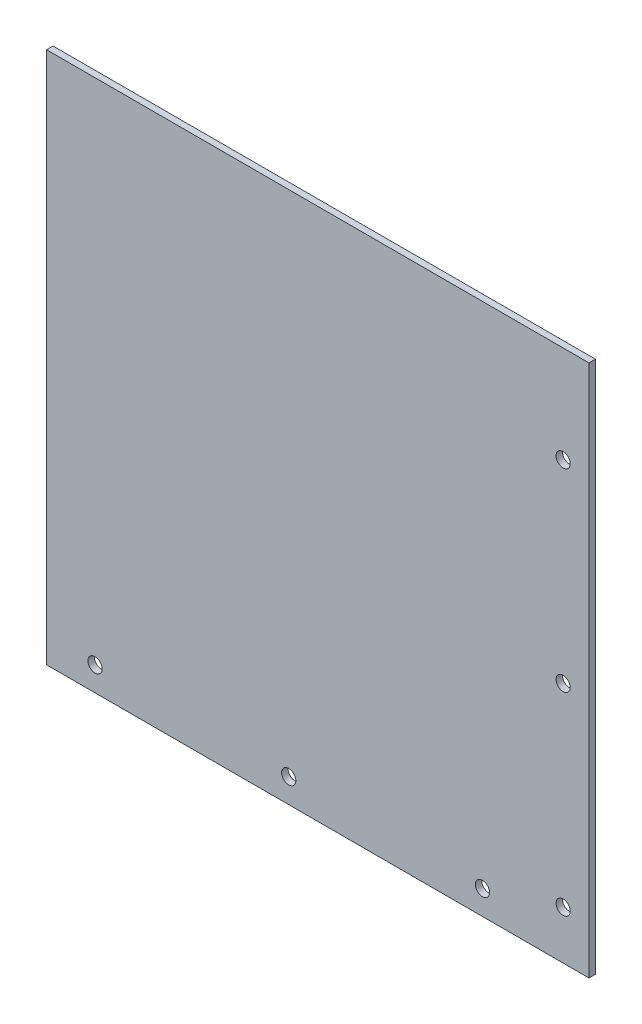
SolidWorks part; units mm, degrees
ref_plane "正面" through (0, 0, 0) normal (0, 0, 1) x (1, 0, 0)
ref_plane "平面" through (0, 0, 0) normal (0, 1, 0) x (1, 0, 0)
ref_plane "右側面" through (0, 0, 0) normal (1, 0, 0) x (0, 0, -1)
sketch "ｽｹｯﾁ1" plane through (0, 0, 0) normal (0, 0, 1) x (1, 0, 0)
  line L1 (-84, 83.5) -> (84, 83.5)
  line L2 (-84, 83.5) -> (-84, -83.5)
  line L3 (-84, -83.5) -> (84, -83.5)
  line L4 (84, 83.5) -> (84, -83.5)
  line L5 (-84, 83.5) -> (84, -83.5) construction
  line L6 (-84, -83.5) -> (84, 83.5) construction
  point P0 (0, 0)
  dimension "D1" = 167
  dimension "D2" = 168
extrude "ﾎﾞｽ - 押し出し1" add sketch "ｽｹｯﾁ1" along normal blind 2
sketch "ｽｹｯﾁ2" plane through (0, 0, 2) normal (0, 0, 1) x (1, 0, 0)
  line L0 (84, -83.5) -> (76, -83.5)
  line L1 (-84, -83.5) -> (84, -83.5) construction
  line L2 (76, -83.5) -> (76, -68.5)
  line L3 (76, -68.5) -> (76, -20.6241)
  line L4 (76, -83.5) -> (76, -8.5)
  line L5 (76, -83.5) -> (76, 51.5)
  circle A0 centre (76, -68.5) radius 2.2
  circle A1 centre (76, -8.5) radius 2.2
  circle A2 centre (76, 51.5) radius 2.2
  dimension "D5" = 4.4
  dimension "D6" = 4.4
  dimension "D7" = 4.4
  dimension "D1" = 8
  dimension "D2" = 15
  dimension "D3" = 75
  dimension "D4" = 135
extrude "ｶｯﾄ - 押し出し1" cut sketch "ｽｹｯﾁ2" against normal blind 2
sketch "ｽｹｯﾁ3" plane through (0, 83.5, 0) normal (0, 1, 0) x (1, 0, 0)
  line L1 (-84, -2) -> (84, -2)
  line L2 (-84, -2) -> (-84, 0)
  line L3 (-84, 0) -> (84, 0)
  line L4 (84, -2) -> (84, 0)
extrude "ｶｯﾄ - 押し出し2" cut sketch "ｽｹｯﾁ3" against normal blind 2
sketch "ｽｹｯﾁ4" plane through (0, 0, 2) normal (0, 0, 1) x (1, 0, 0)
  line L0 (-84, -83.5) -> (-84, -76)
  line L1 (-84, 81.5) -> (-84, -83.5) construction
  line L2 (-84, -76) -> (-69, -76)
  line L3 (-84, -76) -> (-9, -76)
  line L4 (-84, -76) -> (51, -76)
  circle A0 centre (-69, -76) radius 2.2
  circle A1 centre (-9, -76) radius 2.2
  circle A2 centre (51, -76) radius 2.2
  dimension "D5" = 4.4
  dimension "D6" = 4.4
  dimension "D7" = 4.4
  dimension "D1" = 7.5
  dimension "D2" = 15
  dimension "D3" = 75
  dimension "D4" = 135
extrude "ｶｯﾄ - 押し出し3" cut sketch "ｽｹｯﾁ4" against normal blind 2 contours L3 A1 L4 | L4 A1 L3 | L4 A0 L3 | L3 A0 L4 | A2
